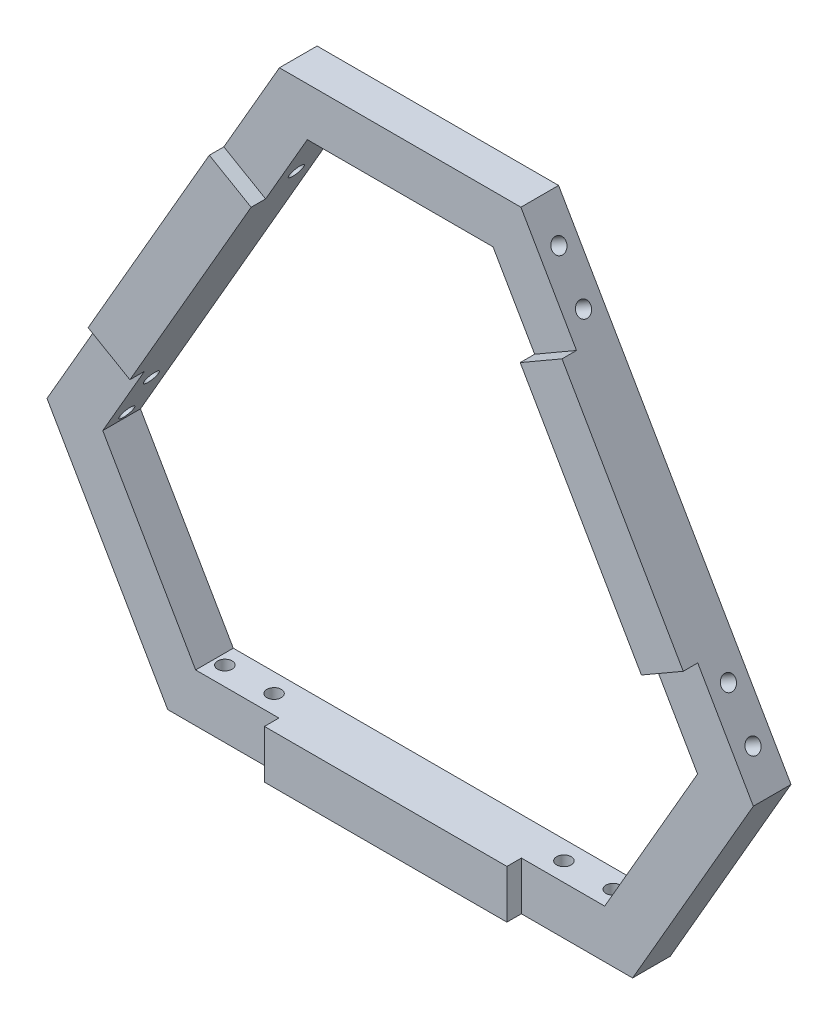
SolidWorks part; units mm, degrees
ref_plane "前基準面" through (0, 0, 0) normal (0, 0, 1) x (1, 0, 0)
ref_plane "上基準面" through (0, 0, 0) normal (0, 1, 0) x (1, 0, 0)
ref_plane "右基準面" through (0, 0, 0) normal (1, 0, 0) x (0, 0, -1)
sketch "草圖1" plane through (0, 0, 0) normal (0, 0, 1) x (1, 0, 0)
  line L0 (0, 0) -> (0, 70) construction
  line L1 (0, 0) -> (60.6218, -35) construction
  line L2 (0, 0) -> (-60.6218, -35) construction
  line L3 (-25, 70) -> (25, 70)
  line L4 (73.1218, -13.3494) -> (48.1218, -56.6506)
  line L5 (-48.1218, -56.6506) -> (-73.1218, -13.3494)
  line L6 (-73.1218, -13.3494) -> (-25, 70)
  line L7 (25, 70) -> (73.1218, -13.3494)
  line L8 (48.1218, -56.6506) -> (-48.1218, -56.6506)
  point P6 (0, 0)
  point P15 (0, 0)
  dimension "D1" = 3
  dimension "D2" = 70
  dimension "D3" = 50
  dimension "D5" = 3
extrude "填料-伸長1" add sketch "草圖1" along normal blind 7.8
sketch "草圖3" plane through (-49.0609, 28.3253, 0) normal (-0.866, 0.5, 0) x (0, 0, 1)
  line L0 (3.9, 48.1218) -> (3.9, -48.1218) construction
  line L1 (7.8, 48.1218) -> (0, 48.1218) construction
  line L2 (7.8, -48.1218) -> (0, -48.1218) construction
  line L3 (0, 0) -> (7.1154, 0) construction
  circle A0 centre (3.9, 40.2) radius 1.5
  circle A1 centre (3.9, 30) radius 1.5
  circle A2 centre (3.9, -30) radius 1.5
  circle A3 centre (3.9, -40.2) radius 1.5
  dimension "D1" = 3
  dimension "D2" = 3
  dimension "D3" = 10.2
  dimension "D4" = 30
extrude "除料-伸長1" cut sketch "草圖3" against normal blind 12
sketch "草圖9" plane through (0, -56.6506, 0) normal (0, -1, 0) x (1, 0, 0)
  line L0 (-48.1218, 3.9) -> (48.1218, 3.9) construction
  line L1 (-48.1218, 7.8) -> (-48.1218, 0) construction
  line L2 (48.1218, 7.8) -> (48.1218, 0) construction
  line L3 (0, 7.8) -> (0, 0) construction
  line L4 (-48.1218, 7.8) -> (48.1218, 7.8) construction
  circle A0 centre (-30, 3.9) radius 1.5
  circle A1 centre (-40.2, 3.9) radius 1.5
  circle A2 centre (40.2, 3.9) radius 1.5
  circle A3 centre (30, 3.9) radius 1.5
  dimension "D1" = 10.2
  dimension "D2" = 3
  dimension "D3" = 3
  dimension "D4" = 30
extrude "除料-伸長2" cut sketch "草圖9" against normal blind 12
sketch "草圖10" plane through (49.0609, 28.3253, 0) normal (0.866, 0.5, 0) x (0, 0, -1)
  line L0 (-3.9, 48.1218) -> (-3.9, -48.1218) construction
  line L1 (-7.8, 48.1218) -> (0, 48.1218) construction
  line L2 (-7.8, -48.1218) -> (0, -48.1218) construction
  line L3 (0, 0) -> (-7.8, 0) construction
  line L4 (-7.8, -48.1218) -> (-7.8, 48.1218) construction
  circle A0 centre (-3.9, 40.2) radius 1.5
  circle A1 centre (-3.9, 30) radius 1.5
  circle A2 centre (-3.9, -30) radius 1.5
  circle A3 centre (-3.9, -40.2) radius 1.5
  dimension "D1" = 10.2
  dimension "D2" = 30
  dimension "D3" = 3
  dimension "D4" = 3
extrude "除料-伸長3" cut sketch "草圖10" against normal blind 12
sketch "草圖11" plane through (0, 0, 7.8) normal (0, 0, 1) x (1, 0, 0)
  line L0 (0, 0) -> (0, 70) construction
  line L1 (25, 70) -> (-25, 70) construction
  line L2 (0, 0) -> (60.6218, -35) construction
  line L3 (48.1218, -56.6506) -> (73.1218, -13.3494) construction
  line L4 (0, 0) -> (0, -56.6506) construction
  line L5 (-48.1218, -56.6506) -> (48.1218, -56.6506) construction
sketch "草圖12" plane through (0, 0, 7.8) normal (0, 0, 1) x (1, 0, 0)
  line L0 (0, 70) -> (0, 0) construction
  line L1 (0, 0) -> (60.6218, -35) construction
sketch "草圖13" plane through (0, 0, 7.8) normal (0, 0, 1) x (1, 0, 0)
  line L0 (-19.2265, 60) -> (19.2265, 60)
  line L1 (19.2265, 60) -> (61.5748, -13.3494)
  line L2 (-25, 70) -> (25, 70)
  line L3 (25, 70) -> (73.1218, -13.3494)
  line L4 (73.1218, -13.3494) -> (48.1218, -56.6506)
  line L5 (-48.1218, -56.6506) -> (48.1218, -56.6506) construction
  line L6 (48.1218, -56.6506) -> (-48.1218, -56.6506)
  line L7 (-48.1218, -56.6506) -> (-73.1218, -13.3494)
  line L8 (-73.1218, -13.3494) -> (-25, 70)
  line L9 (61.5748, -13.3494) -> (42.3483, -46.6506)
  line L10 (42.3483, -46.6506) -> (-42.3483, -46.6506)
  line L11 (-42.3483, -46.6506) -> (-61.5748, -13.3494)
  line L12 (-61.5748, -13.3494) -> (-19.2265, 60)
  dimension "D1" = 10
extrude "除料-伸長4" cut sketch "草圖13" against normal through all contours L12 L11 L10 L9 L1 L0
sketch "草圖14" plane through (0, 0, 7.8) normal (0, 0, 1) x (1, 0, 0)
  line L0 (42.3483, -46.6506) -> (-42.3483, -46.6506) construction
  line L1 (-25.1, -46.6506) -> (25.1, -46.6506)
  line L2 (-25.1, -46.6506) -> (-25.1, -56.6506)
  line L3 (-25.1, -56.6506) -> (25.1, -56.6506)
  line L4 (25.1, -46.6506) -> (25.1, -56.6506)
  line L5 (-48.1218, -56.6506) -> (48.1218, -56.6506) construction
  line L6 (0, 0) -> (0, -56.6506) construction
  line L7 (-25.1, -46.6506) -> (25.1, -46.6506)
  line L8 (25.1, -56.6506) -> (-25.1, -56.6506)
  line L9 (0, 0) -> (-40.4006, 23.3253) construction
  line L11 (0, 0) -> (40.4006, 23.3253) construction
  line L12 (19.2265, 60) -> (61.5748, -13.3494) construction
  line L13 (-61.5748, -13.3494) -> (-19.2265, 60) construction
  line L14 (-36.5109, 50.0626) -> (-27.8506, 45.0626)
  line L15 (-25, 70) -> (-73.1218, -13.3494) construction
  line L16 (-27.8506, 45.0626) -> (-52.9506, 1.5881)
  line L17 (-52.9506, 1.5881) -> (-61.6109, 6.5881)
  line L18 (-61.6109, 6.5881) -> (-36.5109, 50.0626)
  line L19 (27.8506, 45.0626) -> (36.5109, 50.0626)
  line L20 (73.1218, -13.3494) -> (25, 70) construction
  line L21 (36.5109, 50.0626) -> (61.6109, 6.5881)
  line L22 (61.6109, 6.5881) -> (52.9506, 1.5881)
  line L23 (52.9506, 1.5881) -> (27.8506, 45.0626)
  line M1 (-25, 70) -> (-73.1218, -13.3494)
  line M3 (-48.1218, -56.6506) -> (48.1218, -56.6506)
  line M5 (73.1218, -13.3494) -> (25, 70)
  line M7 (-61.5748, -13.3494) -> (-19.2265, 60)
  line M9 (19.2265, 60) -> (61.5748, -13.3494)
  line M11 (42.3483, -46.6506) -> (-42.3483, -46.6506)
  dimension "D1" = 25.1
  dimension "D2" = 25.1
  dimension "D3" = 25.1
  dimension "D4" = 25.1
  dimension "D5" = 25.1
  dimension "D6" = 25.1
extrude "填料-伸長2" add sketch "草圖14" along normal blind 3 contours L17 L14 M7 M1 | L22 L19 M5 M9 | L4 L2 M11 M3
